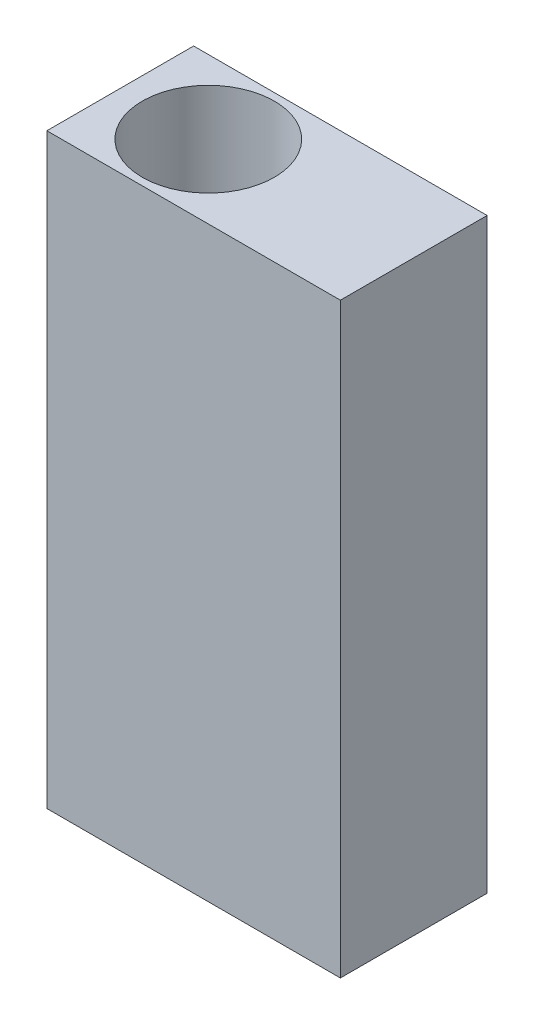
SolidWorks part; units mm, degrees
ref_plane "Front Plane" through (0, 0, 0) normal (0, 0, 1) x (1, 0, 0)
ref_plane "Top Plane" through (0, 0, 0) normal (0, 1, 0) x (1, 0, 0)
ref_plane "Right Plane" through (0, 0, 0) normal (1, 0, 0) x (0, 0, -1)
sketch "Sketch1" plane through (0, 0, 0) normal (0, 1, 0) x (1, 0, 0)
  line L1 (-6, 5) -> (14, 5)
  line L2 (-6, 5) -> (-6, -5)
  line L3 (-6, -5) -> (14, -5)
  line L4 (14, 5) -> (14, -5)
  circle A1 centre (0, 0) radius 4.5
  point P9 (0, 0)
  dimension "D1" = 9
  dimension "D2" = 6
  dimension "D3" = 5
  dimension "D4" = 5
  dimension "D5" = 20
extrude "Boss-Extrude1" add sketch "Sketch1" along normal blind 40
